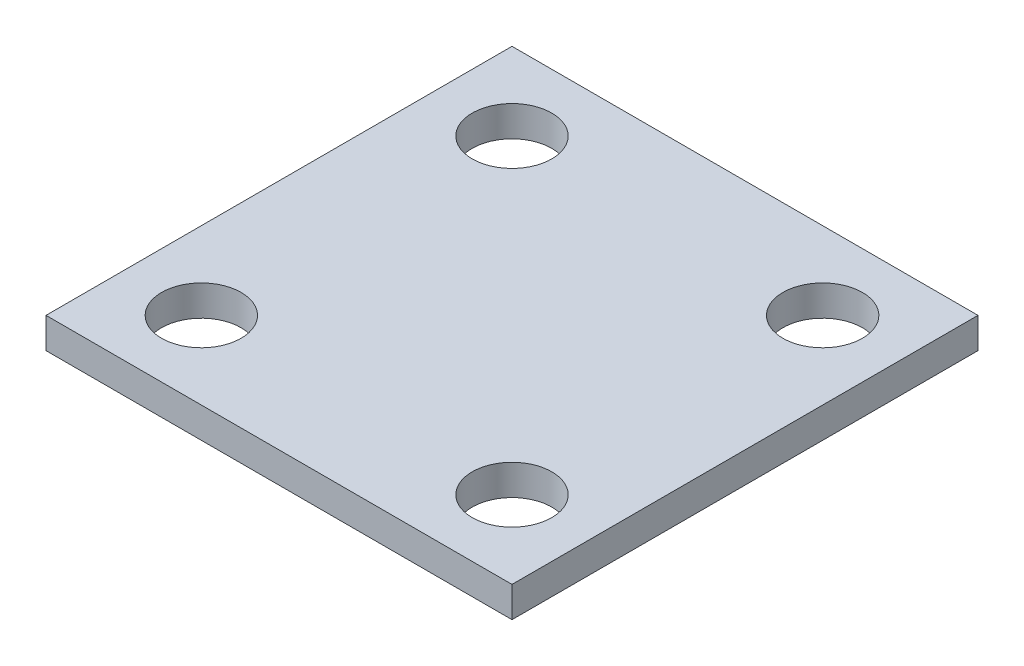
SolidWorks part; units mm, degrees
ref_plane "Front Plane" through (0, 0, 0) normal (0, 0, 1) x (1, 0, 0)
ref_plane "Top Plane" through (0, 0, 0) normal (0, 1, 0) x (1, 0, 0)
ref_plane "Right Plane" through (0, 0, 0) normal (1, 0, 0) x (0, 0, -1)
sketch "Sketch1" plane through (0, 0, 0) normal (0, 1, 0) x (1, 0, 0)
  line L0 (0, -2.7539) -> (0, 5.4568) construction
  line L1 (-19.05, 19.05) -> (19.05, 19.05)
  line L2 (-19.05, 19.05) -> (-19.05, -19.05)
  line L3 (-19.05, -19.05) -> (19.05, -19.05)
  line L4 (19.05, 19.05) -> (19.05, -19.05)
  line L5 (-19.05, 19.05) -> (19.05, -19.05) construction
  line L6 (-19.05, -19.05) -> (19.05, 19.05) construction
  line L7 (-10.9647, 0) -> (8.8737, 0) construction
  circle A0 centre (-12.7, 12.7) radius 3.25
  circle A1 centre (12.7, 12.7) radius 3.25
  circle A2 centre (-12.7, -12.7) radius 3.25
  circle A3 centre (12.7, -12.7) radius 3.25
  point P0 (0, 0)
  dimension "D3" = 6.5
  dimension "D1" = 38.1
  dimension "D2" = 38.1
  dimension "D4" = 6.35
  dimension "D5" = 6.35
extrude "Boss-Extrude1" add sketch "Sketch1" along normal blind 2.5 contours L3 L4 L1 L2
ref_plane "Plane1" through (0, 12.5, 0) normal (0, 1, 0) x (1, 0, 0)
ref_plane "Plane2" through (0, 0, 0) normal (1, 0, 0) x (0, 0, -1)
